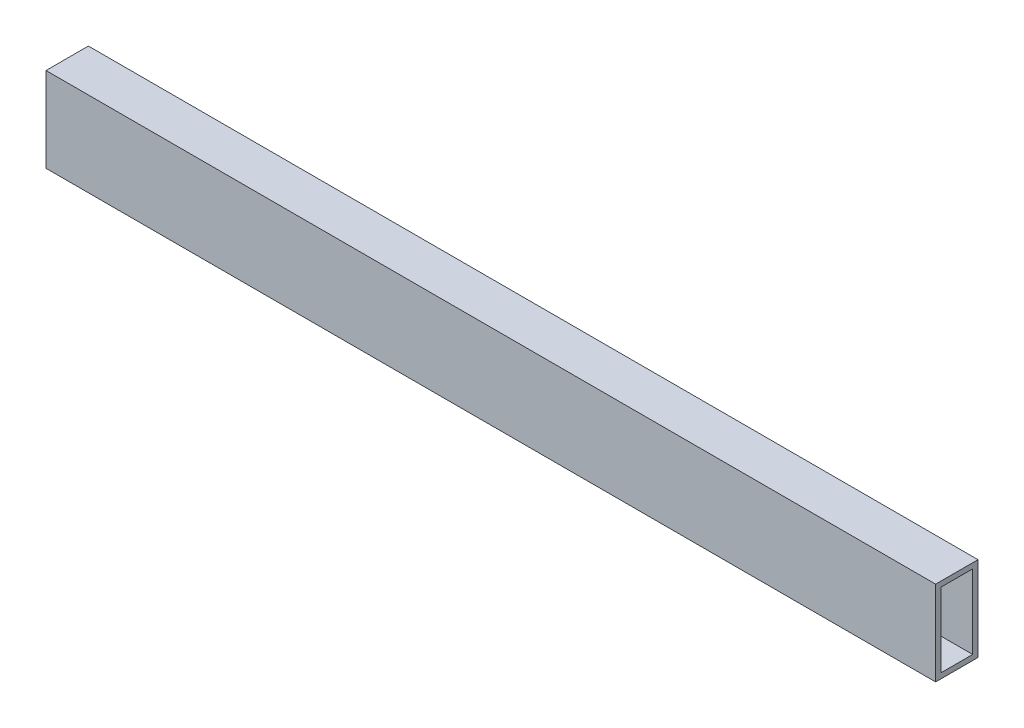
SolidWorks part; units mm, degrees
ref_plane "Front Plane" through (0, 0, 0) normal (0, 0, 1) x (1, 0, 0)
ref_plane "Top Plane" through (0, 0, 0) normal (0, 1, 0) x (1, 0, 0)
ref_plane "Right Plane" through (0, 0, 0) normal (1, 0, 0) x (0, 0, -1)
sketch "Sketch1" plane through (0, 0, 0) normal (1, 0, 0) x (0, 0, -1)
  line L1 (0, 0) -> (25.4, 0)
  line L2 (0, 0) -> (0, 50.8)
  line L3 (0, 50.8) -> (25.4, 50.8)
  line L4 (25.4, 0) -> (25.4, 50.8)
  line L5 (3.175, 47.625) -> (22.225, 47.625)
  line L6 (3.175, 47.625) -> (3.175, 3.175)
  line L7 (3.175, 3.175) -> (22.225, 3.175)
  line L8 (22.225, 47.625) -> (22.225, 3.175)
  dimension "D1" = 3.175
  dimension "D2" = 3.175
  dimension "D3" = 3.175
  dimension "D4" = 3.175
  dimension "D5" = 25.4
  dimension "D6" = 50.8
extrude "Boss-Extrude1" add sketch "Sketch1" along normal blind 533.4
